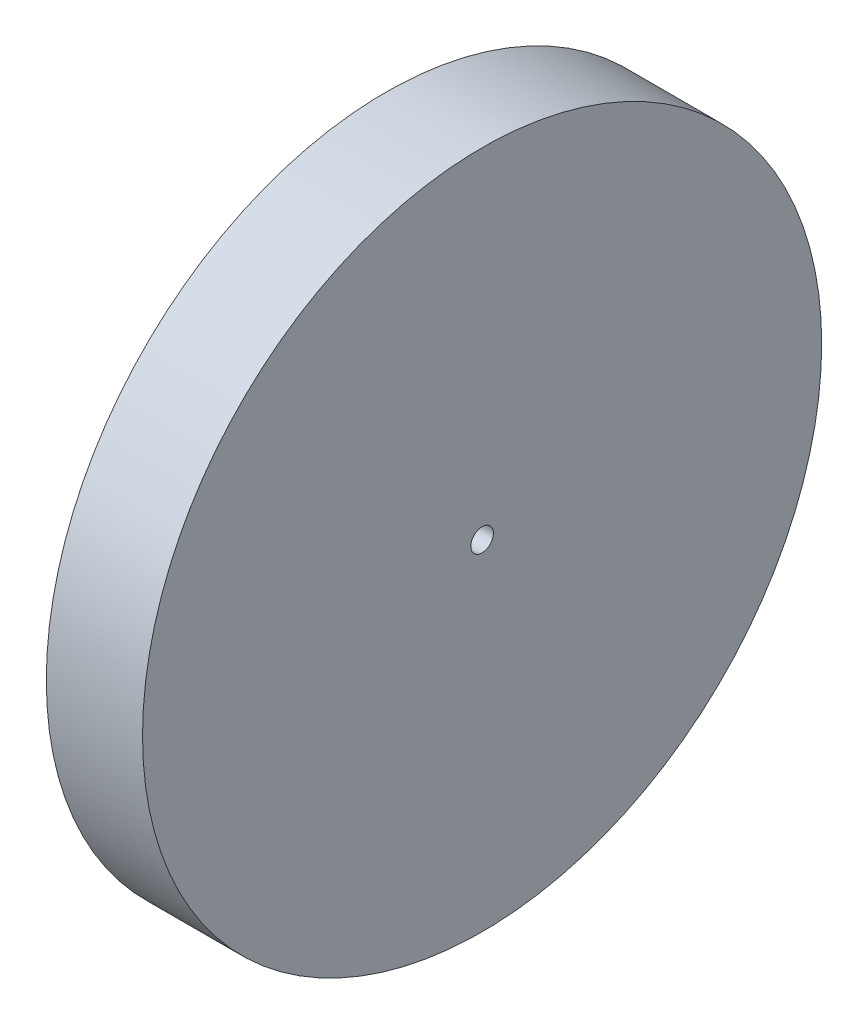
SolidWorks part; units mm, degrees
ref_plane "Plane1" through (0, 0, 0) normal (0, 0, 1) x (1, 0, 0)
ref_plane "Plane2" through (0, 0, 0) normal (0, 1, 0) x (1, 0, 0)
ref_plane "Plane3" through (0, 0, 0) normal (1, 0, 0) x (0, 0, -1)
sketch "HoldingSke" plane through (0, 0, 0) normal (0, 1, 0) x (1, 0, 0)
  line L0 (0, 0) -> (0.3214, -0.383)
  line L1 (-15, 0) -> (100, 0) construction
  line L2 (0, 0) -> (-2.1039, 2.3779)
  line L3 (0, 0) -> (-11.863, 4.5341)
  line L4 (0, 0) -> (5.5511, 6.6156)
  line L5 (0, 0) -> (-23.7986, -8.8762)
  line L6 (0, 0) -> (-10.5278, -7.1032)
  line L7 (-2.1039, 2.3779) -> (3.3635, 27.1825)
  line L8 (-76.2, 4.3779) -> (-54.61, 4.3779)
  line L9 (-71.009, 38.7566) -> (-53.1078, 45.2721)
  line L10 (-76.2, 71.12) -> (104.1128, 71.12)
  line L11 (0, 0) -> (-12, 0)
  line L12 (-76.2, 101.6) -> (-76.133, 101.6)
  line L13 (24.9733, 27.94) -> (52.9518, 28.4284)
  line L14 (24.9733, 27.94) -> (24.9743, 27.94)
  line L15 (24.9733, 27.94) -> (100.4006, 29.5858)
  circle A0 centre (0, 0) radius 60
  circle A1 centre (0, 0) radius 12.7
  circle A2 centre (0, 0) radius 12.7
  dimension "MHD" = 25.4
  dimension "Hub_dia" = 25.4
  dimension "Diameter" = 120
  dimension "Num_teeth" = 50
  dimension "Pitch_radius" = 180.3128
  dimension "Pitch" = 0.5
  dimension "Width" = 12
  dimension "Overall_len" = 25.4
  dimension "Show_teeth" = 50
  dimension "Thickness" = 12.7
  dimension "OAL" = 25.4001
  dimension "T_dim" = 21.59
  dimension "Ap" = 20
  dimension "H" = 19.05
  dimension "Backlash" = 0.067
  dimension "Addendum_fac" = 1
  dimension "Dedendum_fac" = 1.25
  dimension "Clearance_fac" = 0.25
  dimension "Dedendum_add" = 0.001
  dimension "Module" = 2
sketch "BasProSke" plane through (0, 0, 0) normal (0, 1, 0) x (1, 0, 0)
  line L0 (-10, 0) -> (60, 0) construction
  line L1 (0, 48) -> (0, 60)
  line L2 (0, 48) -> (12, 48)
  line L3 (12, 48) -> (12, 60)
  line L4 (12, 60) -> (0, 60)
  dimension "Diameter" = 120
  dimension "Thickness" = 12
  dimension "Inside_diameter" = 96
revolve "Base-Revolve" add sketch "BasProSke" angle 360 about L0
sketch "TooCutSke" plane through (0, 0, 0) normal (1, 0, 0) x (0, 0, -1)
  line L3 (1.738, 49.9698) -> (1.738, 53.6633) construction
  line L4 (0, 0) -> (0, 59.563) construction
  line L5 (0, 0) -> (-4.2903, 68.1927) construction
  line L6 (-21.6015, 41.0107) -> (35.113, 44.5789) construction
  circle A0 centre (0, 0) radius 50 construction
  circle A1 centre (0, 0) radius 52.501 construction
  circle A2 centre (0, 0) radius 42.2862 construction
  circle A3 centre (0, 0) radius 47.9746 construction
  arc A4 (2.4267, 47.9132) -> (0.6033, 52.4975) centre (-21.6015, 41.0107) ccw
  arc A5 (2.4267, 47.9132) -> (-2.4267, 47.9132) centre (0, 0) ccw
  arc A6 (0.6033, 52.4975) -> (-0.6033, 52.4975) centre (0, 0) ccw
  arc A7 (-0.6033, 52.4975) -> (-2.4267, 47.9132) centre (21.6015, 41.0107) ccw
  dimension "Pitch_dia" = 100
  dimension "Base_dia" = 84.5723
  dimension "Root_dia" = 105.002
  dimension "Overcut_dia" = 95.9492
  dimension "Flank_rad" = 25
  dimension "Half_ang" = 3.6
  dimension "Half_CT" = 1.738
extrude "ToothCut" cut sketch "TooCutSke" along normal through all
fillet "Breaks" [suppressed] radius 0.2
fillet "RootFillets" [suppressed] radius 0.501
pattern_circular "TeethCuts" count 50 over 360 about axis through (0, 0, 0) along (1, 0, 0) of "RootFillets", "Breaks", "ToothCut"
sketch "Esquisse1" plane through (12, 0, 0) normal (1, 0, 0) x (0, 0, -1)
  circle A0 centre (0, 0) radius 60
  circle A1 centre (0, 0) radius 2
  dimension "D1" = 120
  dimension "D2" = 4
extrude "Boss.-Extru.1" add sketch "Esquisse1" along normal blind 5
sketch "Esquisse2" plane through (17, 0, 0) normal (1, 0, 0) x (0, 0, -1)
  circle A0 centre (0, 0) radius 60
  circle A1 centre (0, 0) radius 55
  dimension "D1" = 5
  dimension "D2" = 120
extrude "Enlèv. mat.-Extru.1" [suppressed] cut sketch "Esquisse2" against normal up to next
equation "' \"Module@HoldingSke\" = 6.35"
equation "' \"Num_teeth@HoldingSke\" = 24"
equation "' \"Ap@HoldingSke\" =  14.5"
equation "' \"Width@HoldingSke\" = 12"
equation "' \"Diameter@HoldingSke\" = 8 * 25.4"
equation "' \"Show_teeth@HoldingSke\" = 100"
equation "' \"Backlash@HoldingSke\" = 0.009 * 25.4"
equation "' \"Addendum_fac@HoldingSke\" = 1.0"
equation "' \"Dedendum_fac@HoldingSke\" = 1.25"
equation "' \"Dedendum_add@HoldingSke\" = 0.00005 * 25.4"
equation "' \"Clearance_fac@HoldingSke\" = 0.25"
equation "\"Pitch@HoldingSke\" = 1 / \"Module@HoldingSke\" "
equation "\"Overcut_dia@TooCutSke\" = (\"Num_teeth@HoldingSke\" - 2 * \"Addendum_fac@HoldingSke\") / \"Pitch@HoldingSke\" - 0.002 * 25.4"
equation "\"Pitch_dia@TooCutSke\" = \"Num_teeth@HoldingSke\" / \"Pitch@HoldingSke\""
equation "\"Base_dia@TooCutSke\" = \"Num_teeth@HoldingSke\" / \"Pitch@HoldingSke\" * cos((\"Ap@HoldingSke\"  * 3.14159265 / 180)) * 0.90"
equation "\"Root_dia@TooCutSke\" = \"Num_teeth@HoldingSke\"  / \"Pitch@HoldingSke\" + 2 *  \"Dedendum_fac@HoldingSke\"/ \"Pitch@HoldingSke\" + \"Dedendum_add@HoldingSke\" * 2"
equation "\"Half_ang@TooCutSke\" = 180 / \"Num_teeth@HoldingSke\""
equation "\"Half_CT@TooCutSke\" = \"Num_teeth@HoldingSke\" / \"Pitch@HoldingSke\" * sin((3.14159265 / 2 / \"Num_teeth@HoldingSke\")) / 2 + 10 * \"Backlash@HoldingSke\" / 4"
equation "\"Flank_rad@TooCutSke\" = \"Num_teeth@HoldingSke\" / \"Pitch@HoldingSke\" / 4"
equation "\"Radius@RootFillets\"= \"Clearance_fac@HoldingSke\" / \"Pitch@HoldingSke\" + \"Dedendum_add@HoldingSke\""
equation "\"Break_rad@Breaks\" = 0.02 / \"Pitch@HoldingSke\" * 5"
equation "\"Num_teeth@TeethCuts\" = int( \"Show_teeth@HoldingSke\" ) + 1"
equation "\"Num_teeth@TeethCuts\" = ((sgn( \"Num_teeth@TeethCuts\" - \"Num_teeth@HoldingSke\" )-1)*( \"Num_teeth@TeethCuts\" - \"Num_teeth@HoldingSke\" ))/-2+ \"Num_teeth@HoldingSke\""
equation "\"Num_teeth@TeethCuts\" = ((sgn( \"Num_teeth@TeethCuts\" - 2.0)+1)*( \"Num_teeth@TeethCuts\" - 2.0))/2 +2.0"
equation "\"Angle@TeethCuts\" = 360.0 / \"Num_teeth@HoldingSke\""
equation "\"Diameter@BasProSke\" = \"Num_teeth@HoldingSke\"  / \"Pitch@HoldingSke\" + 2 *  \"Dedendum_fac@HoldingSke\"/ \"Pitch@HoldingSke\" + \"Dedendum_add@HoldingSke\" * 2 + 0.002 * 25.4"
equation "\"Diameter@BasProSke\" = ((sgn( \"Diameter@BasProSke\"  - \"Diameter@HoldingSke\" )+1)*( \"Diameter@BasProSke\"  - \"Diameter@HoldingSke\" ))/2 + \"Diameter@HoldingSke\""
equation "\"Inside_diameter@BasProSke\" =  (\"Num_teeth@HoldingSke\" - 2 * \"Addendum_fac@HoldingSke\") / \"Pitch@HoldingSke\" "
equation "\"Thickness@BasProSke\"  = \"Width@HoldingSke\""
